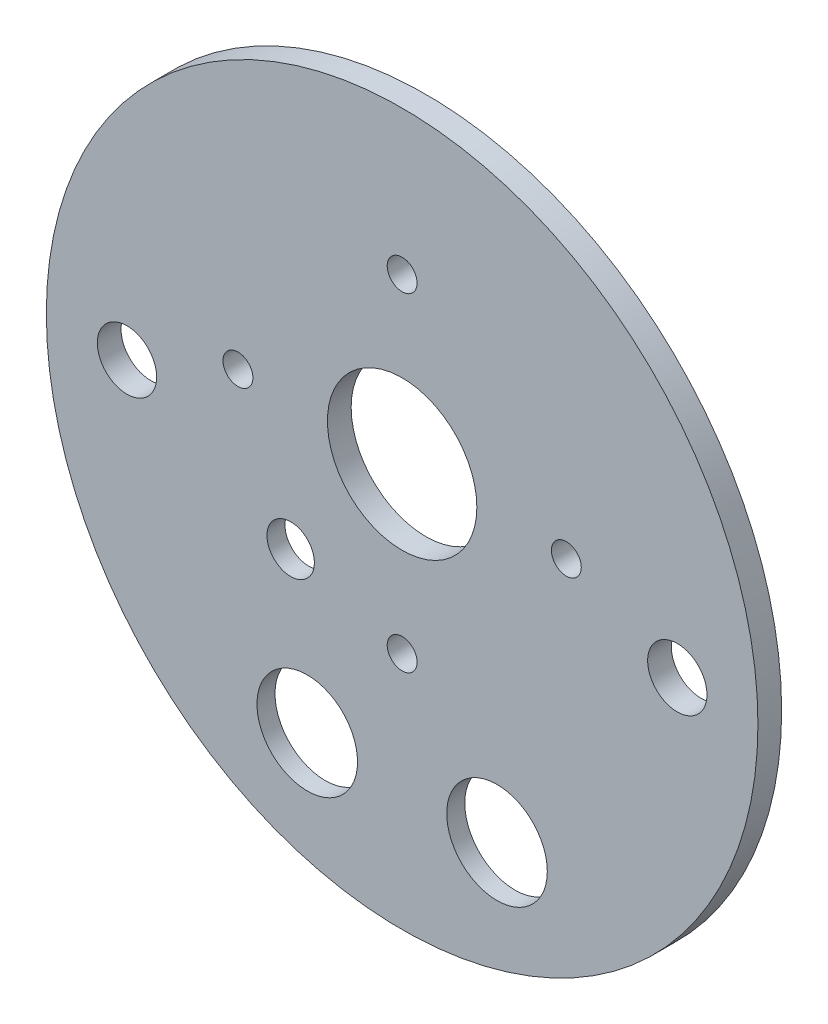
SolidWorks part; units mm, degrees
ref_plane "Front Plane" through (0, 0, 0) normal (0, 0, 1) x (1, 0, 0)
ref_plane "Top Plane" through (0, 0, 0) normal (0, 1, 0) x (1, 0, 0)
ref_plane "Right Plane" through (0, 0, 0) normal (1, 0, 0) x (0, 0, -1)
sketch "Sketch1" plane through (0, 0, 0) normal (0, 0, 1) x (1, 0, 0)
  circle A0 centre (0, 0) radius 49.5046
  dimension "D1" = 99.0092
extrude "Boss-Extrude1" add sketch "Sketch1" along normal blind 5.08
sketch "Sketch2" plane through (0, 0, 5.08) normal (0, 0, 1) x (1, 0, 0)
  circle A0 centre (0, 0) radius 47.625
  dimension "D1" = 95.25
extrude "Boss-Extrude2" add sketch "Sketch2" along normal blind 3.175
sketch "Sketch3" plane through (0, 0, 8.255) normal (0, 0, 1) x (1, 0, 0)
  line L0 (-21.9769, 6.35) -> (0, -15.6269) construction
  line L1 (-21.9769, 6.35) -> (0, 28.3269) construction
  line L2 (0, -15.6269) -> (21.9769, 6.35) construction
  line L3 (0, 28.3269) -> (21.9769, 6.35) construction
  line L4 (-7.7384, -11.0295) -> (-21.9624, -11.0295) construction
  line L5 (-7.7384, -12.9345) -> (-8.8833, -12.9345) construction
  line L6 (-7.7384, -9.1245) -> (-8.845, -9.1245) construction
  line L7 (-20.9594, -12.9345) -> (-21.9624, -12.9345) construction
  line L8 (-20.9977, -9.1245) -> (-21.9624, -9.1245) construction
  circle A0 centre (-12.7, -31.1668) radius 6.731
  circle A1 centre (12.7, -31.1668) radius 6.731
  circle A2 centre (-12.7, -31.1668) radius 12.7 construction
  circle A3 centre (12.7, -31.1668) radius 12.7 construction
  circle A4 centre (12.7, -31.1668) radius 13.97 construction
  circle A5 centre (-12.7, -31.1668) radius 13.97 construction
  circle A6 centre (0, 0) radius 47.625 construction
  circle A7 centre (-36.83, 0) radius 3.9687
  circle A8 centre (36.83, 0) radius 3.9687
  circle A9 centre (0, 6.35) radius 15.24 construction
  circle A10 centre (-14.9213, -10.9686) radius 8.89 construction
  circle A11 centre (0, 6.35) radius 16.51 construction
  circle A12 centre (-14.9213, -10.9686) radius 7.62 construction
  circle A13 centre (0, 6.35) radius 10
  arc A14 (-20.9594, -12.9345) -> (-8.8833, -12.9345) centre (-14.9213, -10.9686) ccw construction
  circle A15 centre (0, 28.3269) radius 2
  circle A16 centre (21.9769, 6.35) radius 2
  circle A17 centre (0, -15.6269) radius 2
  circle A18 centre (-21.9769, 6.35) radius 2
  circle A19 centre (0, 6.35) radius 31.55 construction
  arc A24 (-7.7384, -12.9345) -> (-7.7384, -9.1245) centre (-7.7384, -11.0295) ccw construction
  arc A25 (-21.9624, -9.1245) -> (-21.9624, -12.9345) centre (-21.9624, -11.0295) ccw construction
  arc A26 (-8.845, -9.1245) -> (-20.9977, -9.1245) centre (-14.9213, -10.9686) ccw construction
  circle A27 centre (-14.9213, -10.9686) radius 3.175
  point P40 (-14.9213, -10.9686)
  point P47 (-23.8674, -11.0295)
  point P50 (-5.8334, -11.0295)
  dimension "D1" = 13.462
  dimension "D2" = 13.462
  dimension "D3" = 27.94
  dimension "D4" = 27.94
  dimension "D5" = 25.4
  dimension "D6" = 25.4
  dimension "D7" = 7.9375
  dimension "D8" = 7.9375
  dimension "D11" = 30.48
  dimension "D12" = 33.02
  dimension "D13" = 15.24
  dimension "D14" = 17.78
  dimension "D15" = 20
  dimension "D16" = 12.7
  dimension "D18" = 4
  dimension "D23" = 63.1
  dimension "D29" = 6.35
  dimension "D9" = 73.66
  dimension "D10" = 36.83
  dimension "D17" = 6.35
  dimension "D19" = 31.08
  dimension "D20" = 31.08
  dimension "D21" = 31.08
  dimension "D27" = 3.81
  dimension "D28" = 18.034
extrude "Cut-Extrude1" cut sketch "Sketch3" against normal through all
sketch "Sketch4" [suppressed] plane through (0, 0, 6.35) normal (0, 0, 1) x (1, 0, 0)
  circle A0 centre (0, 0) radius 49.5046
  circle A1 centre (0, 0) radius 47.6885
extrude "Boss-Extrude3" [suppressed] add sketch "Sketch4" against normal up to surface (3.175 mm away)
sketch "Sketch5" [suppressed] plane through (0, 0, 6.35) normal (0, 0, 1) x (1, 0, 0)
  circle A0 centre (0, 6.35) radius 11.1125
extrude "Boss-Extrude4" [suppressed] add sketch "Sketch5" against normal up to surface (6.35 mm away)
sketch "Sketch6" [suppressed] plane through (0, 0, 6.35) normal (0, 0, 1) x (1, 0, 0)
  circle A0 centre (-23.622, -17.272) radius 2.54
  circle A1 centre (23.622, -17.272) radius 2.54
extrude "Boss-Extrude5" [suppressed] add sketch "Sketch6" against normal blind 6.35
sketch "Sketch7" plane through (0, 0, 0) normal (0, 0, -1) x (-1, 0, 0)
  circle A0 centre (0, 0) radius 52.1663
extrude "Cut-Extrude4" cut sketch "Sketch7" against normal blind 5.08
sketch "Sketch8" plane through (0, 0, 5.08) normal (0, 0, -1) x (-1, 0, 0)
  circle A0 centre (-12.7, -31.1668) radius 11.176
  circle A1 centre (12.7, -31.1668) radius 11.176
  circle A2 centre (14.9213, -10.9686) radius 6.35
  dimension "D1" = 22.352
  dimension "D2" = 22.352
  dimension "D3" = 12.7
extrude "Cut-Extrude5" cut sketch "Sketch8" against normal blind 0.762
